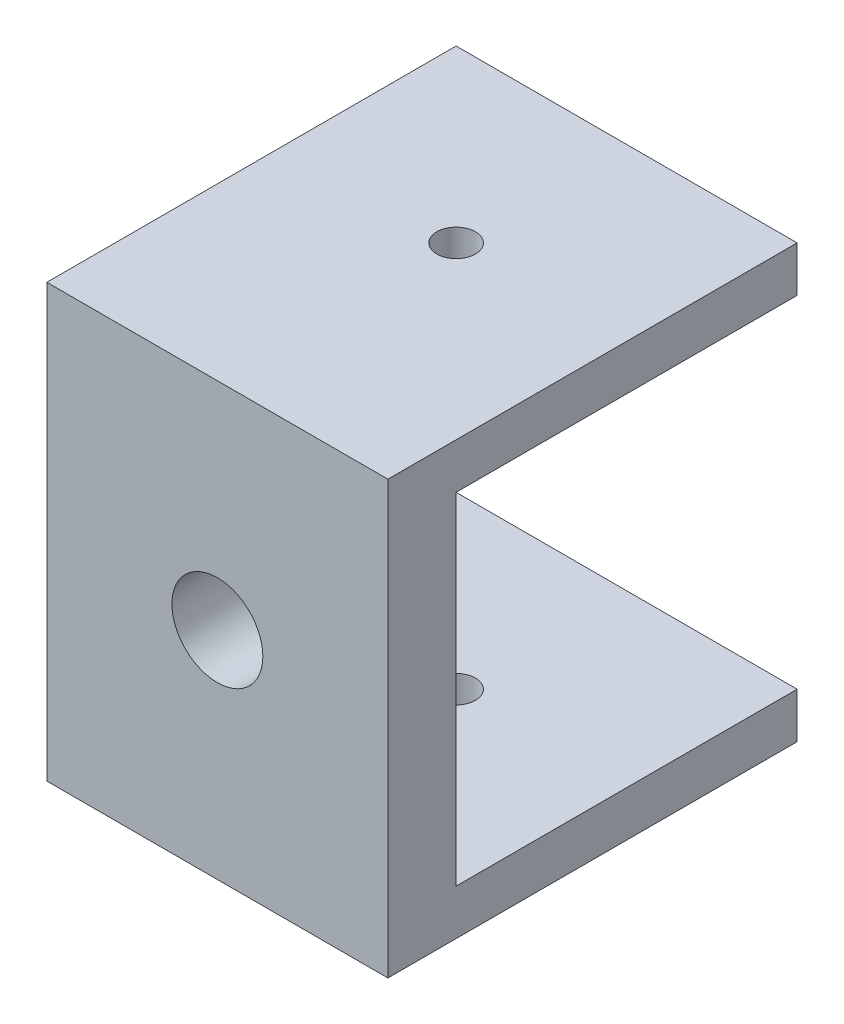
SolidWorks part; units mm, degrees
ref_plane "Front Plane" through (0, 0, 0) normal (0, 0, 1) x (1, 0, 0)
ref_plane "Top Plane" through (0, 0, 0) normal (0, 1, 0) x (1, 0, 0)
ref_plane "Right Plane" through (0, 0, 0) normal (1, 0, 0) x (0, 0, -1)
sketch "Sketch2" plane through (0, 0, 0) normal (1, 0, 0) x (0, 0, -1)
  line L1 (-3, 15) -> (3, 15)
  line L2 (-3, 15) -> (-3, -15)
  line L3 (-3, -15) -> (3, -15)
  line L4 (3, 15) -> (3, -15)
  line L5 (-3, 15) -> (3, -15) construction
  line L6 (-3, -15) -> (3, 15) construction
  line L7 (-3, -15) -> (33, -15)
  line L8 (-3, -15) -> (-3, -19)
  line L9 (-3, -19) -> (33, -19)
  line L10 (33, -15) -> (33, -19)
  line L11 (-3, 15) -> (33, 15)
  line L12 (-3, 15) -> (-3, 19)
  line L13 (-3, 19) -> (33, 19)
  line L14 (33, 15) -> (33, 19)
  point P0 (0, 0)
extrude "Boss-Extrude1" add sketch "Sketch2" along normal blind 30 contours L4 L1 L2 L3 | L11 L14 L13 L12 L1 | L10 L7 L3 L8 L9
sketch "Sketch4" plane through (0, 0, 3) normal (0, 0, 1) x (1, 0, 0)
  line L0 (0, 0) -> (30, 0) construction
  line L1 (0, 19) -> (0, -19) construction
  line L2 (30, 19) -> (30, -19) construction
  circle A0 centre (15, 0) radius 4
extrude "Cut-Extrude2" cut sketch "Sketch4" against normal blind 30
sketch "Sketch5" plane through (0, -19, 0) normal (0, -1, 0) x (1, 0, 0)
  line L0 (15, -33) -> (15, -18) construction
  line L1 (30, -33) -> (0, -33) construction
  circle A0 centre (15, -18) radius 1.7
extrude "Cut-Extrude3" cut sketch "Sketch5" against normal through all
